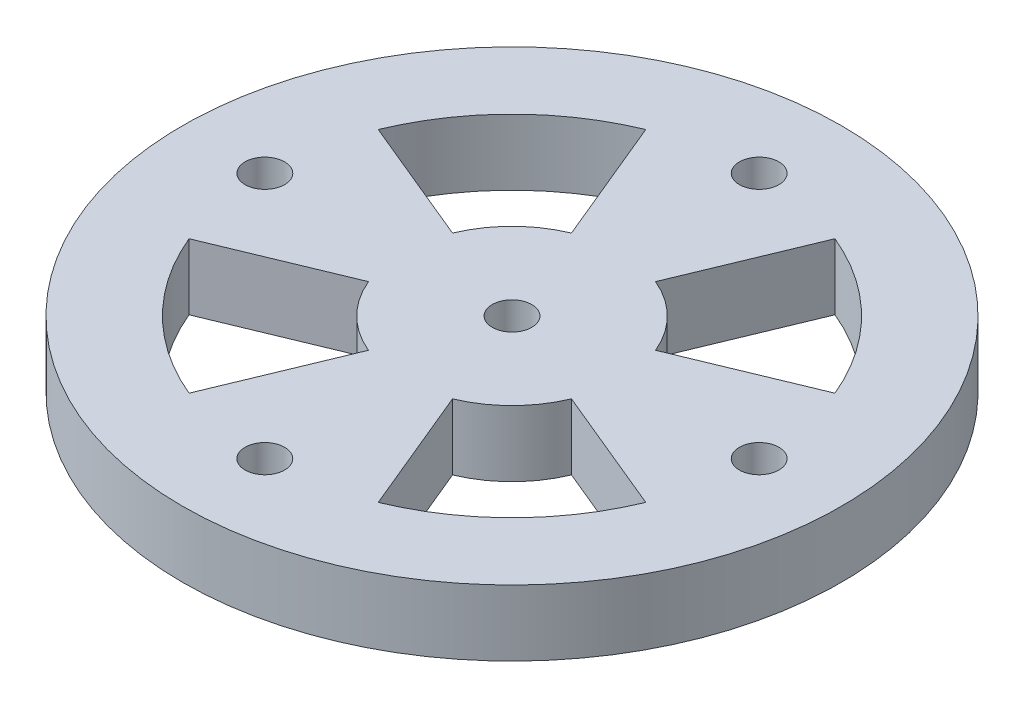
SolidWorks part; units mm, degrees
material "Acrylic (Medium-high impact)"
ref_plane "Front Plane" through (0, 0, 0) normal (0, 0, 1) x (1, 0, 0)
ref_plane "Top Plane" through (0, 0, 0) normal (0, 1, 0) x (1, 0, 0)
ref_plane "Right Plane" through (0, 0, 0) normal (1, 0, 0) x (0, 0, -1)
sketch "Sketch1" plane through (0, 0, 0) normal (0, 1, 0) x (1, 0, 0)
  line L0 (0, -25) -> (0, 25) construction
  line L1 (-25, 0) -> (25, 0) construction
  line L2 (-13.2583, 13.2583) -> (0, 0) construction
  line L3 (7.699, 3.189) -> (17.3227, 7.1753)
  line L4 (3.189, 7.699) -> (7.1753, 17.3227)
  line L5 (3.189, -7.699) -> (7.1753, -17.3227)
  line L6 (7.699, -3.189) -> (17.3227, -7.1753)
  line L9 (-7.699, -3.189) -> (-17.3227, -7.1753)
  line L11 (-3.189, -7.699) -> (-7.1753, -17.3227)
  line L51 (-7.699, 3.189) -> (-17.3227, 7.1753)
  line L52 (-3.189, 7.699) -> (-7.1753, 17.3227)
  circle A1 centre (0, 0) radius 8.3333 construction
  circle A2 centre (0, 0) radius 18.75 construction
  circle A3 centre (0, 0) radius 25
  circle A4 centre (0, 0) radius 1.5
  circle A16 centre (18.75, 0) radius 1.5
  arc A19 (3.189, 7.699) -> (7.699, 3.189) centre (0, 0) cw
  arc A20 (7.1753, 17.3227) -> (17.3227, 7.1753) centre (0, 0) cw
  circle A21 centre (0, -18.75) radius 1.5
  arc A22 (7.699, -3.189) -> (3.189, -7.699) centre (0, 0) cw
  arc A23 (17.3227, -7.1753) -> (7.1753, -17.3227) centre (0, 0) cw
  circle A24 centre (-18.75, 0) radius 1.5
  arc A25 (-3.189, -7.699) -> (-7.699, -3.189) centre (0, 0) cw
  arc A26 (-7.1753, -17.3227) -> (-17.3227, -7.1753) centre (0, 0) cw
  arc A71 (-17.3227, 7.1753) -> (-7.1753, 17.3227) centre (0, 0) cw
  arc A72 (-7.699, 3.189) -> (-3.189, 7.699) centre (0, 0) cw
  circle A73 centre (0, 18.75) radius 1.5
  point P30 (0, 0)
  point P35 (0, 0)
  point P44 (0, 0)
  point P119 (0, 0)
  point P136 (0, 0)
  point P147 (0, 0)
  dimension "D3" = 50
  dimension "D2" = 3
  dimension "D4" = 37.5
  dimension "D5" = 16.6667
  dimension "D6" = 22.5
  dimension "D1" = 45
  dimension "D7" = 45
  dimension "D8" = 4
extrude "Boss-Extrude1" add sketch "Sketch1" along normal blind 5
equation "\"Wheel Diameter\"= 5cm"
equation "\"D3@Sketch1\"=\"Wheel Diameter\""
equation "\"3M screw hole\"= 0.3cm"
equation "\"D2@Sketch1\"=\"3M screw hole\""
equation "\"D4@Sketch1\"=\"Wheel Diameter\"/4*3"
equation "\"D5@Sketch1\"=\"Wheel Diameter\"/3"
